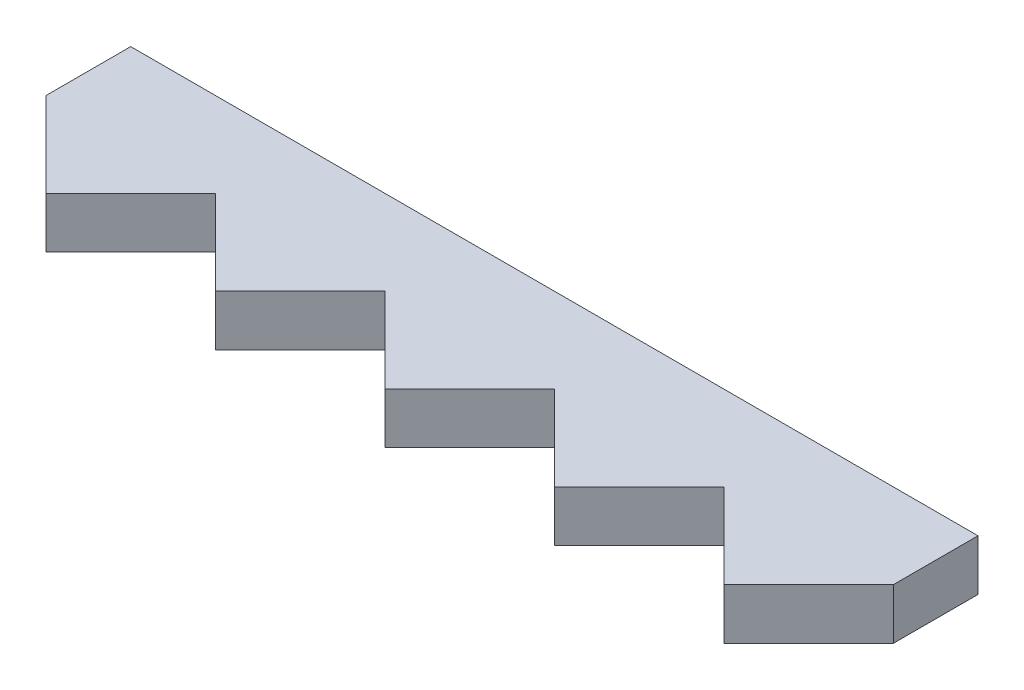
SolidWorks part; units mm, degrees
ref_plane "Front Plane" through (0, 0, 0) normal (0, 0, 1) x (1, 0, 0)
ref_plane "Top Plane" through (0, 0, 0) normal (0, 1, 0) x (1, 0, 0)
ref_plane "Right Plane" through (0, 0, 0) normal (1, 0, 0) x (0, 0, -1)
sketch "Sketch1" plane through (0, 3, 0) normal (0, 1, 0) x (1, 0, 0)
  line L0 (0, 71.6064) -> (0, 66.6064)
  line L2 (0, 66.6064) -> (5, 61.6064)
  line L3 (5, 61.6064) -> (10, 66.6064)
  line L7 (10, 66.6064) -> (15, 61.6064)
  line L8 (15, 61.6064) -> (20, 66.6064)
  line L9 (20, 66.6064) -> (25, 61.6064)
  line L10 (25, 61.6064) -> (30, 66.6064)
  line L11 (30, 66.6064) -> (35, 61.6064)
  line L12 (35, 61.6064) -> (40, 66.6064)
  line L13 (40, 66.6064) -> (45, 61.6064)
  line L14 (45, 61.6064) -> (50, 66.6064)
  line L19 (0, 71.6064) -> (50, 71.6064)
  line L20 (50, 71.6064) -> (50, 66.6064)
  point P2 (0, 0)
  point P3 (5, 25.624)
  point P7 (0, 0)
  point P8 (0, 0)
  point P9 (0, 0)
  point P10 (51.1683, 27.1404)
  point P11 (45.2226, 22.363)
  point P15 (0, 0)
  point P18 (0, 0)
  point P21 (0, 0)
  point P24 (0, 0)
  point P25 (0, 0)
  point P26 (0, 0)
  point P27 (0, 0)
  point P28 (0, 0)
  point P29 (0, 0)
  point P30 (5, 24.3965)
  point P31 (50, 43.929)
  point P32 (0, 39.4297)
  point P33 (0, 0)
  point P34 (35, 35.3361)
  point P35 (35, 35.2254)
  point P36 (50, 64.7702)
  point P37 (0, 0)
  point P38 (0, 0)
  dimension "D1" = 5
  dimension "D2" = 5
  dimension "D3" = 10
  dimension "D4" = 5
extrude "Boss-Extrude1" add sketch "Sketch1" along normal blind 3
